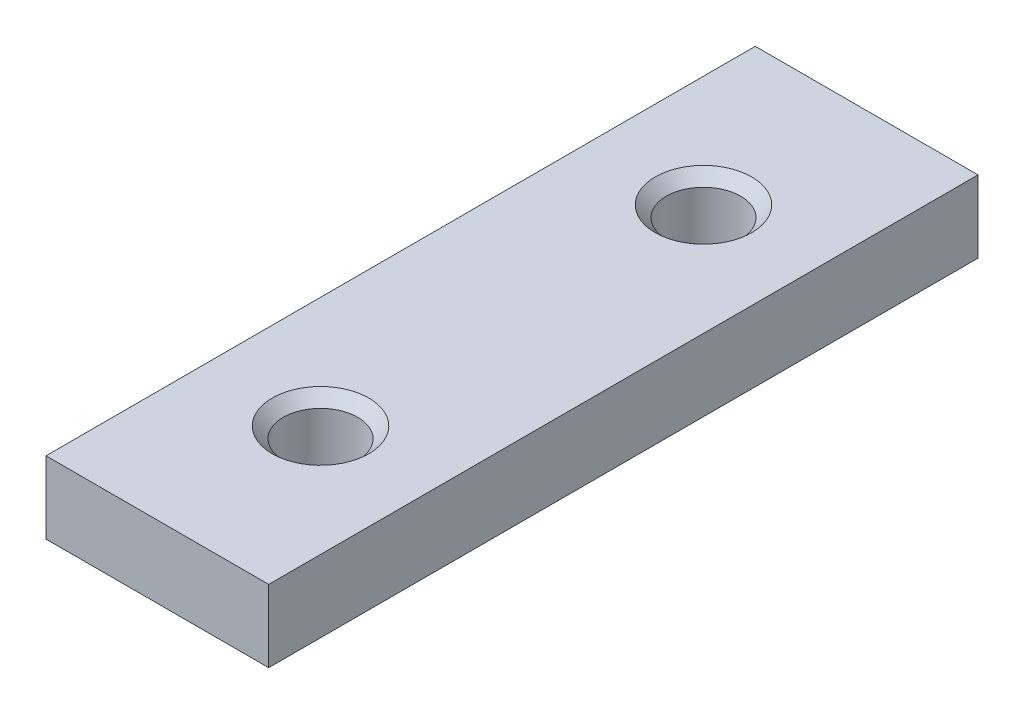
SolidWorks part; units mm, degrees
material "ABS"
ref_plane "Front Plane" through (0, 0, 0) normal (0, 0, 1) x (1, 0, 0)
ref_plane "Top Plane" through (0, 0, 0) normal (0, 1, 0) x (1, 0, 0)
ref_plane "Right Plane" through (0, 0, 0) normal (1, 0, 0) x (0, 0, -1)
sketch "Sketch1" plane through (0, 0, 0) normal (0, 1, 0) x (1, 0, 0)
  line L0 (-0.55, -0.55) -> (-20.6149, -0.55)
  line L1 (0, 0) -> (-21.1649, 0) construction
  line L2 (0, 0) -> (0, -65) construction
  line L3 (0, -65) -> (-21.1649, -65) construction
  line L4 (-21.1649, 0) -> (-21.1649, -65) construction
  line L5 (-20.6149, -0.55) -> (-20.6149, -64.45)
  line L6 (-0.55, -64.45) -> (-20.6149, -64.45)
  line L7 (-0.55, -0.55) -> (-0.55, -64.45)
  line L8 (-10.5824, 0) -> (-10.5824, -65) construction
  line L9 (-21.1649, -32.5) -> (0, -32.5) construction
  line L10 (-22.5705, 0) -> (-22.5705, -32.5)
  line L11 (-22.5705, -15.25) -> (0, -15.25) construction
  line L12 (-21.1649, 2.617) -> (-10.5824, 2.617)
  line L13 (-15.8736, 2.617) -> (-15.8736, -32.5) construction
  circle A0 centre (-10.5824, -15.25) radius 3.35
  circle A1 centre (-10.5824, -49.75) radius 3.35
  point P25 (-22.5705, -16.25)
  dimension "D6" = 6.7
  dimension "D1" = 65
  dimension "D2" = 21.1649
  dimension "D4" = 1.4056
  dimension "D5" = 2.617
  dimension "D7" = 1
  dimension "D3" = 0.55
extrude "Boss-Extrude1" add sketch "Sketch1" along normal blind 6.5 contours L7 L0 L5 L6 A0 A1
chamfer "Chamfer1" distance 1 angle 45 2 edges at (-10.5824, 6.5, 53.1) (-10.5824, 6.5, 18.6)
